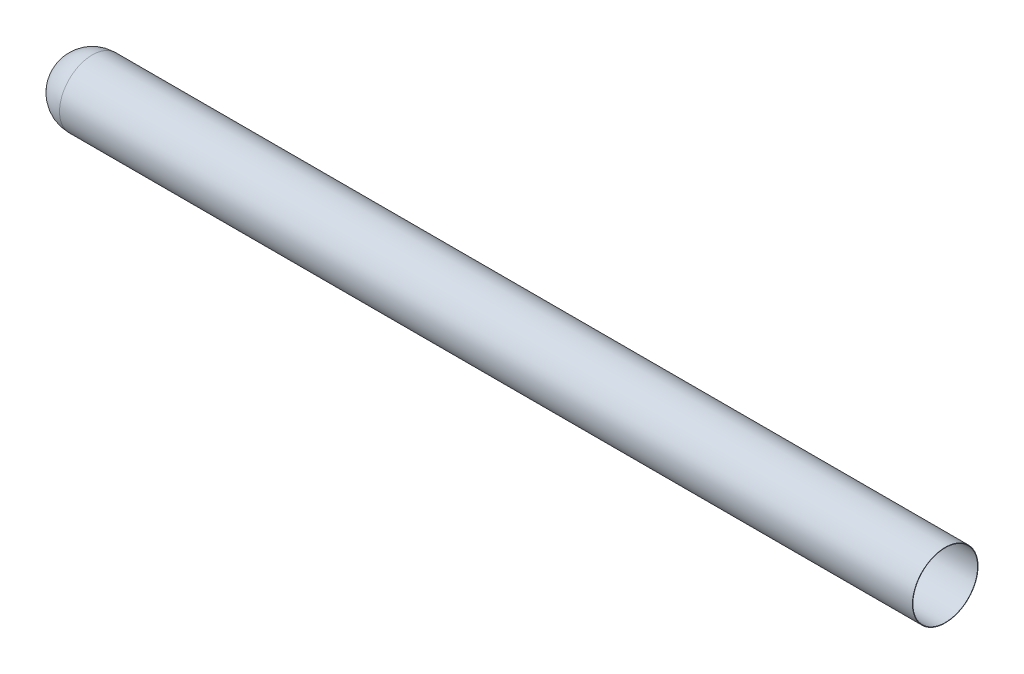
SolidWorks part; units mm, degrees
ref_plane "Front Plane" through (0, 0, 0) normal (0, 0, 1) x (1, 0, 0)
ref_plane "Top Plane" through (0, 0, 0) normal (0, 1, 0) x (1, 0, 0)
ref_plane "Right Plane" through (0, 0, 0) normal (1, 0, 0) x (0, 0, -1)
sketch "rootSketch" plane through (0, 0, 0) normal (0, 1, 0) x (1, 0, 0)
  line L0 (0, 0) -> (12000, 0) construction
  line L1 (250, -250) -> (250, 250) construction
  line L2 (0, 0) -> (6750, 0) construction
  line L3 (250, -250) -> (6750, -250)
  line L4 (6750, -250) -> (6750, 0) construction
  line L5 (6750, -250) -> (6750, -246.825)
  line L6 (6750, -246.825) -> (250, -246.825)
  line L7 (3.175, 0) -> (0, 0)
  arc A1 (250, -250) -> (0, 0) centre (250, 0) cw
  arc A2 (250, -246.825) -> (3.175, 0) centre (250, 0) cw
  point P5 (250, 0)
  dimension "rootMaxThickness" = 500
  dimension "D1" = 6750
  dimension "D2" = 3.175
revolve "Revolve1" add sketch "rootSketch" angle 360 about L0
ref_plane "Plane1" through (5330, 0, 0) normal (1, 0, 0) x (0, 0, -1)
equation "\"D1@rootSketch\" = \"length\""
equation "\"rootMaxThickness@rootSketch\"=\"diameter\""
equation "\"length\"= 6.75"
equation "\"diameter\"= 0.5"
